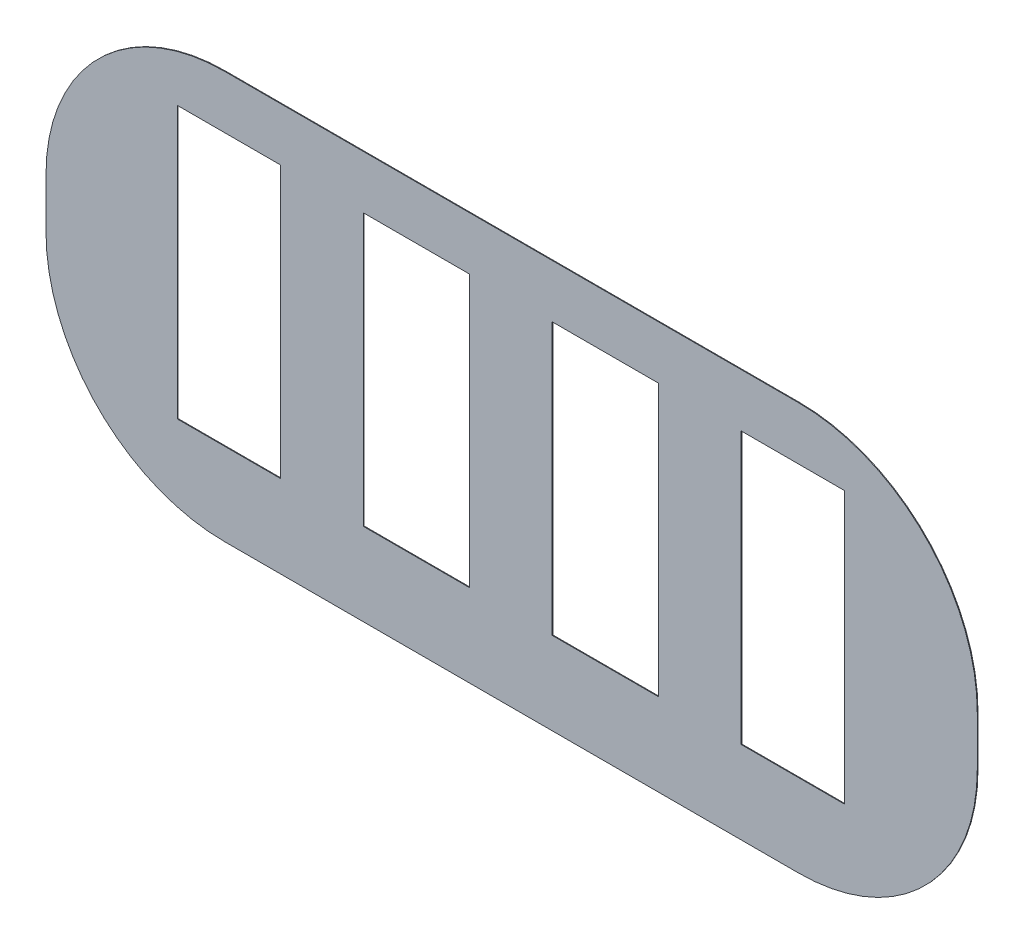
SolidWorks part; units mm, degrees
ref_plane "Front Plane" through (0, 0, 0) normal (0, 0, 1) x (1, 0, 0)
ref_plane "Top Plane" through (0, 0, 0) normal (0, 1, 0) x (1, 0, 0)
ref_plane "Right Plane" through (0, 0, 0) normal (1, 0, 0) x (0, 0, -1)
sketch "Sketch1" plane through (0, 0, 0) normal (0, 0, 1) x (1, 0, 0)
  line L1 (3.0734, 0) -> (12.954, 0)
  line L2 (0, 3.0734) -> (0, 3.937)
  line L3 (3.0734, 7.0104) -> (12.954, 7.0104)
  line L4 (16.0274, 3.0734) -> (16.0274, 3.937)
  arc A0 (12.954, 0) -> (16.0274, 3.0734) centre (12.954, 3.0734) ccw
  arc A1 (12.954, 7.0104) -> (16.0274, 3.937) centre (12.954, 3.937) cw
  arc A2 (3.0734, 0) -> (0, 3.0734) centre (3.0734, 3.0734) cw
  arc A3 (0, 3.937) -> (3.0734, 7.0104) centre (3.0734, 3.937) cw
  point P11 (0, 0)
  dimension "D3" = 3.0734
  dimension "D1" = 16.0274
  dimension "D2" = 7.0104
extrude "Boss-Extrude1" add sketch "Sketch1" along normal blind 0.0127
sketch "Sketch2" plane through (0, 0, 0.0127) normal (0, 0, 1) x (1, 0, 0)
  line L1 (2.2606, 6.096) -> (4.0386, 6.096)
  line L2 (2.2606, 6.096) -> (2.2606, 1.4224)
  line L3 (2.2606, 1.4224) -> (4.0386, 1.4224)
  line L4 (4.0386, 6.096) -> (4.0386, 1.4224)
  line L5 (0, 3.937) -> (0, 3.0734) construction
  line L6 (15.977, 3.5052) -> (0, 3.5052) construction
  line L7 (12.954, 7.0104) -> (3.0734, 7.0104) construction
  dimension "D1" = 1.778
  dimension "D2" = 4.6736
  dimension "D3" = 2.0828
  dimension "D4" = 2.2606
  dimension "D5" = 3.5052
extrude "Cut-Extrude1" cut sketch "Sketch2" against normal through all
pattern_linear "LPattern1" count 2 spacing 3.2004 along (1, 0, 0) of "Cut-Extrude1"
pattern_linear "LPattern2" count 3 spacing 3.2512 along (1, 0, 0) of "LPattern1", "Cut-Extrude1"
